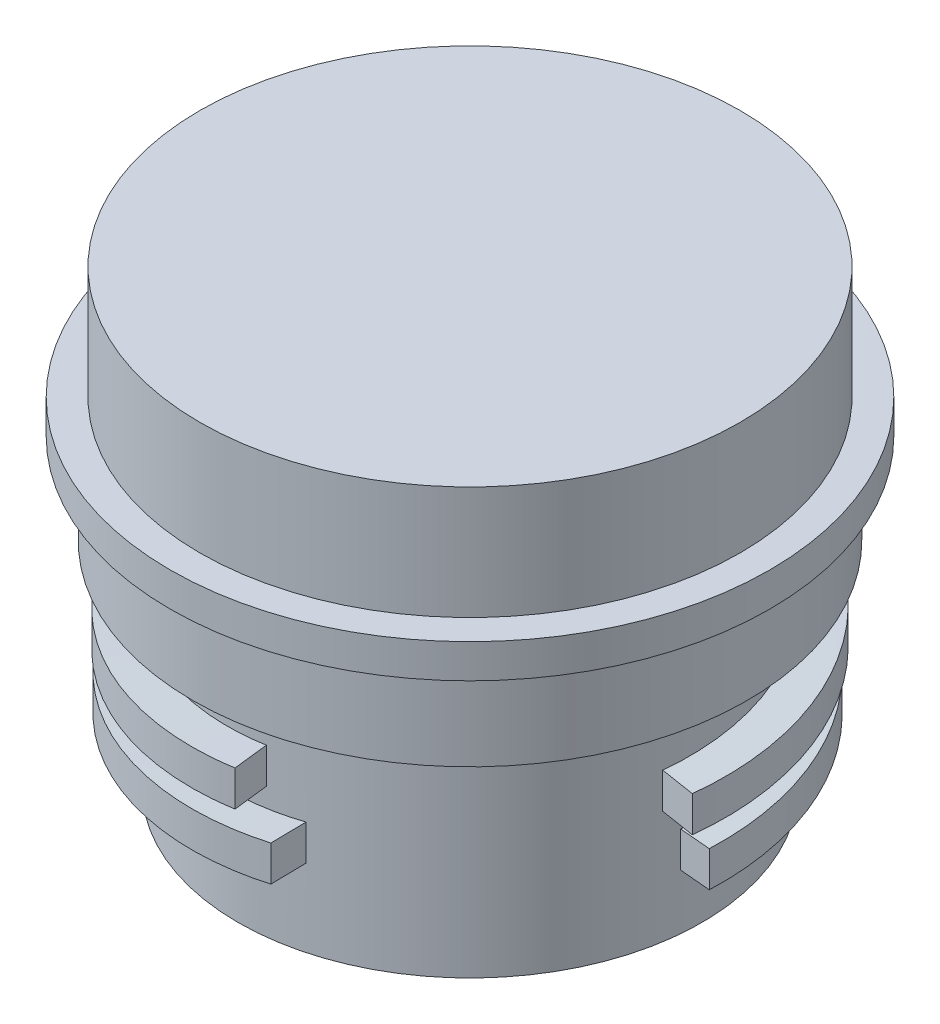
SolidWorks part; units mm, degrees
ref_plane "Front Plane" through (0, 0, 0) normal (0, 0, 1) x (1, 0, 0)
ref_plane "Top Plane" through (0, 0, 0) normal (0, 1, 0) x (1, 0, 0)
ref_plane "Right Plane" through (0, 0, 0) normal (1, 0, 0) x (0, 0, -1)
sketch "Sketch1" plane through (0, 0, 0) normal (0, 1, 0) x (1, 0, 0)
  circle A0 centre (0, 0) radius 20.5
  dimension "D1" = 41
extrude "Boss-Extrude1" add sketch "Sketch1" along normal blind 19
sketch "Sketch2" plane through (0, 19, 0) normal (0, 1, 0) x (1, 0, 0)
  circle A0 centre (0, 0) radius 24.5
  dimension "D1" = 49
extrude "Boss-Extrude2" add sketch "Sketch2" along normal blind 8
sketch "Sketch3" plane through (0, 27, 0) normal (0, 1, 0) x (1, 0, 0)
  circle A0 centre (0, 0) radius 26.5
  dimension "D1" = 53
extrude "Boss-Extrude3" add sketch "Sketch3" along normal blind 3
sketch "Sketch4" plane through (0, 30, 0) normal (0, 1, 0) x (1, 0, 0)
  circle A0 centre (0, 0) radius 23.8864
extrude "Boss-Extrude4" add sketch "Sketch4" along normal blind 10
ref_plane "Plane1" through (0, 6.25, 0) normal (0, -1, 0) x (-1, 0, 0)
sketch "Sketch5" plane through (0, 6.25, 0) normal (0, -1, 0) x (-1, 0, 0)
  circle A0 centre (0, 0) radius 20.5
curve "Helix/Spiral1" pitch 6.35 height 2.2225 turns 0.35
sketch "Sketch7" plane through (0, 6.25, 0) normal (0, -1, 0) x (-1, 0, 0)
  circle A0 centre (0, 0) radius 20.5
curve "Helix/Spiral2" pitch 6.35 height 2.2225 turns 0.35
ref_plane "Plane2" through (0, 11.25, 0) normal (0, -1, 0) x (-1, 0, 0)
sketch "Sketch8" plane through (0, 11.25, 0) normal (0, -1, 0) x (-1, 0, 0)
  circle A0 centre (0, 0) radius 20.5
curve "Helix/Spiral3" pitch 6.35 height 1.9685 turns 0.31
sketch "Sketch9" plane through (0, 11.25, 0) normal (0, -1, 0) x (-1, 0, 0)
  circle A1 centre (0, 0) radius 20.5
curve "Helix/Spiral4" pitch 6.35 height 1.9685 turns 0.31
sketch "Sketch10" plane through (0, 0, 0) normal (0, 0, 1) x (1, 0, 0)
  line L1 (-17.6003, 12.9956) -> (-23.65, 12.9956)
  line L2 (-17.6003, 12.9956) -> (-17.6003, 9.8456)
  line L3 (-17.6003, 9.8456) -> (-23.65, 9.8456)
  line L4 (-23.65, 12.9956) -> (-23.65, 9.8456)
  line L5 (-17.6003, 12.9956) -> (-23.65, 9.8456) construction
  line L6 (-17.6003, 9.8456) -> (-23.65, 12.9956) construction
  line L7 (-20.5, 19) -> (-20.5, 0) construction
  point P5 (-21.5384, 9.8386)
  point P9 (0, 0)
  point P12 (0, 0)
  dimension "D1" = 3.15
  dimension "D2" = 3.15
sweep "Sweep1" add profiles "Sketch10" path "Helix/Spiral4"
ref_plane "Plane3" through (0, 0, 5) normal (0, 0, 1) x (1, 0, 0)
sketch "Sketch11" plane through (0, 0, 5) normal (0, 0, 1) x (1, 0, 0)
  line L1 (-17.5236, 8.4019) -> (-23.0448, 8.4019)
  line L2 (-17.5236, 8.4019) -> (-17.5236, 5.2519)
  line L3 (-17.5236, 5.2519) -> (-23.0448, 5.2519)
  line L4 (-23.0448, 8.4019) -> (-23.0448, 5.2519)
  line L5 (-17.5236, 8.4019) -> (-23.0448, 5.2519) construction
  line L6 (-17.5236, 5.2519) -> (-23.0448, 8.4019) construction
  spline S0 degree 3 poles (-19.1384, 6.25) (-19.9046, 6.3554) (-20.8129, 6.5677) (-20.1295, 6.8849) (-17.4779, 7.2025) (-13.1153, 7.52) (-7.4674, 7.8376) (-1.0946, 8.1548) (3.2407, 8.3671) (5.3058, 8.4725) knots 0 0 0 0 0.142857 0.285714 0.428571 0.571429 0.714286 0.857143 1 1 1 1 construction
  point P0 (-19.8948, 6.8666)
  point P5 (0, 0)
  point P6 (0, 0)
  point P7 (-19.9208, 5.1524)
  point P8 (0, 0)
  point P9 (0, 0)
  point P12 (0, 0)
  point P13 (-19.8756, 6.4116)
  point P14 (0, 0)
  point P15 (0, 0)
  point P16 (-19.8948, 6.8666)
  dimension "D1" = 3.15
  dimension "D2" = 3.15
sweep "Sweep2" add profiles "Sketch11" path "Helix/Spiral1"
sketch "Sketch18" plane through (0, 0, 0) normal (0, 0, 1) x (1, 0, 0)
  line L1 (16.9729, 8.1073) -> (23.2729, 8.1073)
  line L2 (16.9729, 8.1073) -> (16.9729, 4.9573)
  line L3 (16.9729, 4.9573) -> (23.2729, 4.9573)
  line L4 (23.2729, 8.1073) -> (23.2729, 4.9573)
  line L5 (16.9729, 8.1073) -> (23.2729, 4.9573) construction
  line L6 (16.9729, 4.9573) -> (23.2729, 8.1073) construction
  spline S0 degree 3 poles (20.422, 6.25) (20.6083, 6.3554) (20.3062, 6.5677) (17.8633, 6.8849) (13.6722, 7.2025) (8.1431, 7.52) (1.8154, 7.8376) (-4.6845, 8.1548) (-8.7257, 8.3671) (-10.5583, 8.4725) knots 0 0 0 0 0.142857 0.285714 0.428571 0.571429 0.714286 0.857143 1 1 1 1 construction
  point P0 (20.1229, 6.5323)
  point P7 (20.4826, 6.2969)
  point P8 (20.5, 6.3388)
  point P9 (0, 0)
  point P10 (20.422, 6.25)
  dimension "D1" = 3.15
  dimension "D2" = 3.15
sweep "Sweep3" add profiles "Sketch18" path "Helix/Spiral2"
sketch "Sketch19" plane through (0, 0, 0) normal (0, 0, 1) x (1, 0, 0)
  line L0 (20.5, 8.1065) -> (20.5, 19) construction
  line L1 (17.35, 13.3113) -> (23.65, 13.3113)
  line L2 (17.35, 13.3113) -> (17.35, 10.1613)
  line L3 (17.35, 10.1613) -> (23.65, 10.1613)
  line L4 (23.65, 13.3113) -> (23.65, 10.1613)
  line L5 (17.35, 13.3113) -> (23.65, 10.1613) construction
  line L6 (17.35, 10.1613) -> (23.65, 13.3113) construction
  line L7 (20.5, 8.1065) -> (20.5, 19) construction
  point P0 (20.5, 11.7363)
  point P5 (20.5, 10.4154)
  point P7 (0, 0)
  point P8 (0, 0)
  point P10 (0, 0)
  point P11 (20.5, 11.7363)
  dimension "D1" = 3.15
  dimension "D2" = 3.15
sweep "Sweep4" add profiles "Sketch19" path "Helix/Spiral3"
